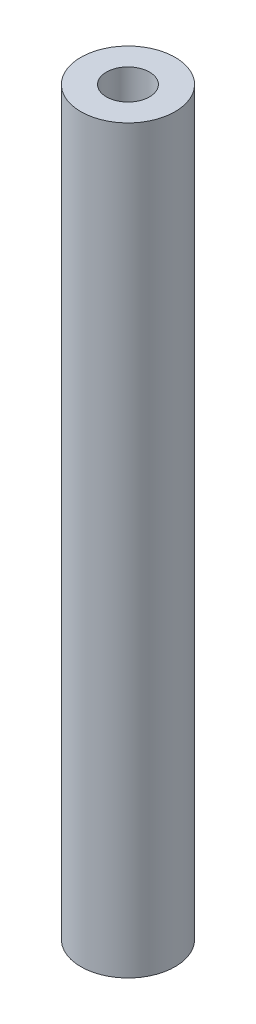
SolidWorks part; units mm, degrees
ref_plane "正面" through (0, 0, 0) normal (0, 0, 1) x (1, 0, 0)
ref_plane "平面" through (0, 0, 0) normal (0, 1, 0) x (1, 0, 0)
ref_plane "右側面" through (0, 0, 0) normal (1, 0, 0) x (0, 0, -1)
sketch "ｽｹｯﾁ1" plane through (0, 0, 0) normal (0, 1, 0) x (1, 0, 0)
  circle A0 centre (0, 0) radius 3.5
extrude "ﾎﾞｽ - 押し出し1" add sketch "ｽｹｯﾁ1" along normal blind 55
sketch "ｽｹｯﾁ2" plane through (0, 55, 0) normal (0, 1, 0) x (1, 0, 0)
  circle A0 centre (0, 0) radius 1.6
extrude "ｶｯﾄ - 押し出し1" cut sketch "ｽｹｯﾁ2" against normal through all
